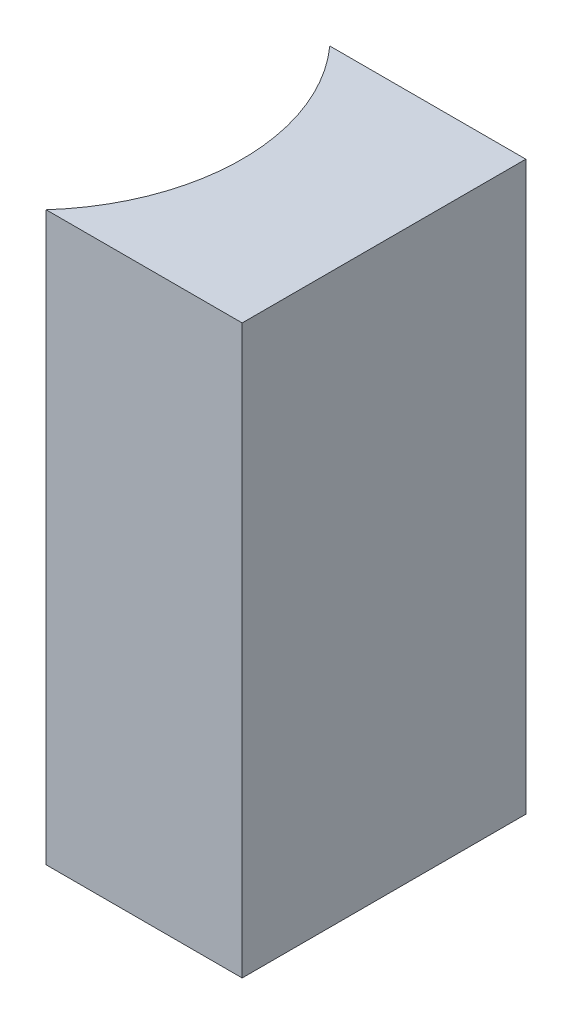
SolidWorks part; units mm, degrees
ref_plane "前视基准面" through (0, 0, 0) normal (0, 0, 1) x (1, 0, 0)
ref_plane "上视基准面" through (0, 0, 0) normal (0, 1, 0) x (1, 0, 0)
ref_plane "右视基准面" through (0, 0, 0) normal (1, 0, 0) x (0, 0, -1)
sketch "草图1" plane through (0, 0, 0) normal (0, 1, 0) x (1, 0, 0)
  line L0 (0, 0) -> (0, -4)
  line L1 (0, 0) -> (-2.7639, 0)
  line L2 (0, -4) -> (-2.7639, -4)
  line L3 (4.224, -2) -> (-5.9059, -2) construction
  arc A0 (-2.7639, -4) -> (-2.7639, 0) centre (-5, -2) ccw
  point P7 (-2, -2)
  point P8 (0, -2)
  dimension "D2" = 3
  dimension "D3" = 2
  dimension "D1" = 4
extrude "凸台-拉伸1" add sketch "草图1" along normal blind 8
